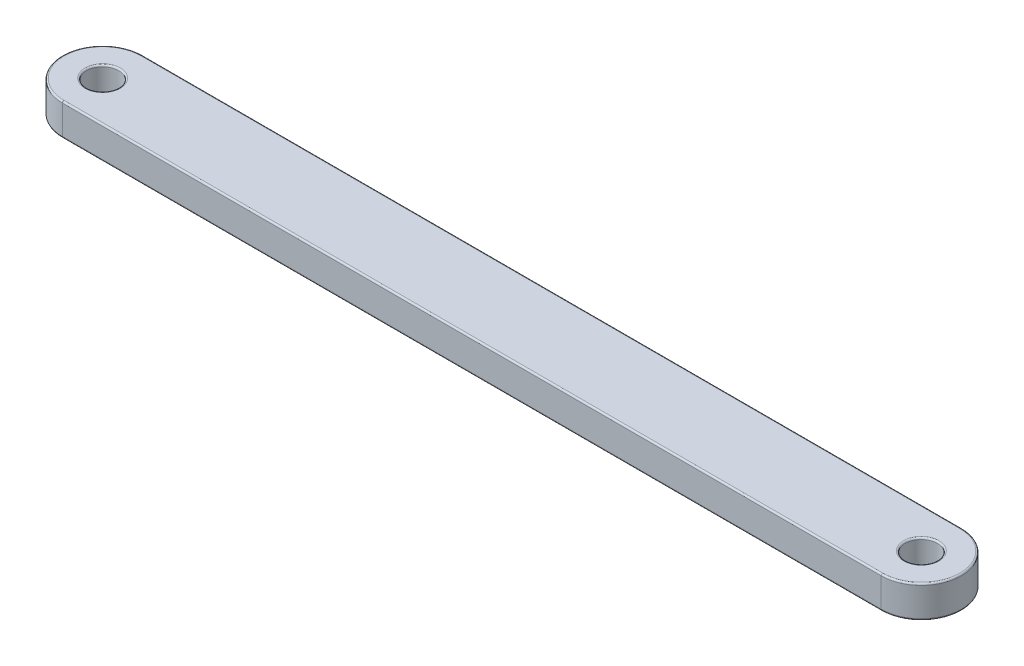
SolidWorks part; units mm, degrees
material "Alloy Steel"
ref_plane "Front Plane" through (0, 0, 0) normal (0, 0, 1) x (1, 0, 0)
ref_plane "Top Plane" through (0, 0, 0) normal (0, 1, 0) x (1, 0, 0)
ref_plane "Right Plane" through (0, 0, 0) normal (1, 0, 0) x (0, 0, -1)
sketch "Sketch1" plane through (0, 0, 0) normal (0, 1, 0) x (1, 0, 0)
  line L0 (-255, 0) -> (255, 0) construction
  line L1 (-255, 25) -> (255, 25)
  line L2 (-255, -25) -> (255, -25)
  line L3 (0, 0) -> (0, 241.5958) construction
  arc A0 (-255, 25) -> (-255, -25) centre (-255, 0) ccw
  arc A1 (255, -25) -> (255, 25) centre (255, 0) ccw
  circle A2 centre (-255, 0) radius 10
  circle A3 centre (255, 0) radius 10
  point P2 (0, 0)
  dimension "D2" = 20
  dimension "D3" = 50
  dimension "D1" = 510
extrude "Boss-Extrude1" add sketch "Sketch1" along normal blind 20
fillet "Fillet1" radius 1 12 edges at (255, 0, -10) (-255, 0, 10) (0, 0, 25) (280, 0, 0) (0, 0, -25) (-280, 0, 0) (255, 20, -10) (0, 20, -25) (280, 20, 0) (0, 20, 25) (-280, 20, 0) (-255, 20, 10)
scale "Scale1" scale about centroid uniform scaling yes scale factor 0.125
